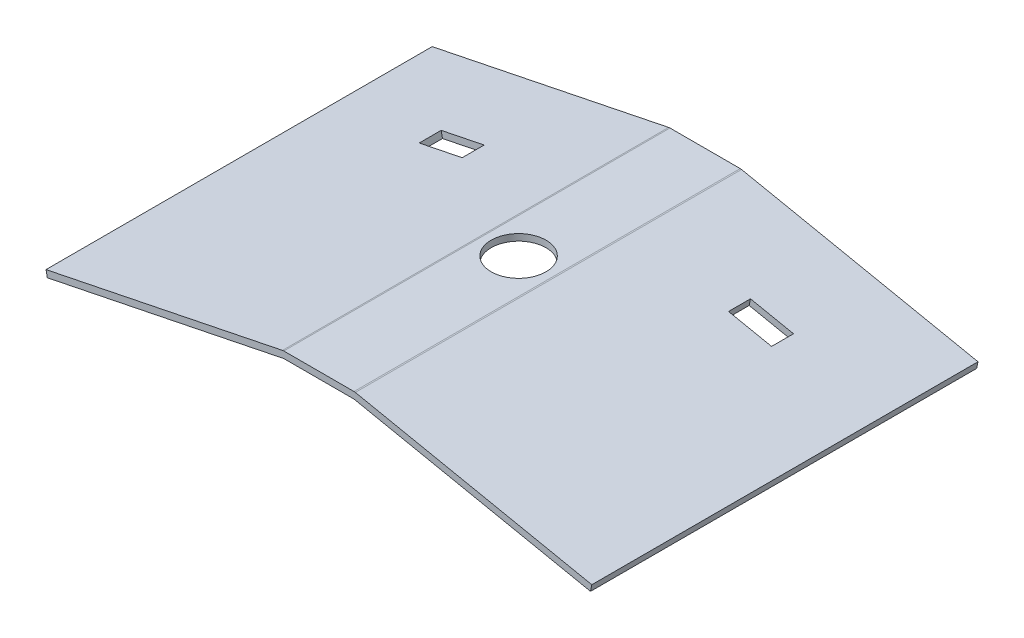
SolidWorks part; units mm, degrees
ref_plane "Front Plane" through (0, 0, 0) normal (0, 0, 1) x (1, 0, 0)
ref_plane "Top Plane" through (0, 0, 0) normal (0, 1, 0) x (1, 0, 0)
ref_plane "Right Plane" through (0, 0, 0) normal (1, 0, 0) x (0, 0, -1)
sketch "Sketch1" plane through (0, 0, 0) normal (0, 0, 1) x (1, 0, 0)
  line L0 (0, 0) -> (0, 19.9998) construction
  line L1 (-16, 19.9998) -> (16, 19.9998)
  line L2 (-113.9796, 0) -> (-113.9796, -10)
  line L4 (113.9796, 0) -> (113.9796, -10)
  line L6 (-113.9796, -7.3549) -> (0, 0) construction
  line L7 (0, 19.9998) -> (0, -10) construction
  line L8 (0, -10) -> (0, 0) construction
  line L9 (0, 0) -> (-113.9796, 0) construction
  line L10 (-113.9796, 0) -> (113.9796, 0) construction
  line L11 (-113.9796, 0) -> (-16, 19.9998)
  line L12 (16, 19.9998) -> (113.9796, 0)
  line L13 (-113.9796, -10) -> (113.9796, -10)
  point P0 (0, 0)
  dimension "D1" = 16
  dimension "D2" = 227.9593
  dimension "D3" = 100
  dimension "D4" = 10
extrude "Boss-Extrude1" add sketch "Sketch1" along normal blind 3
sketch "Sketch2" plane through (0, 0, 3) normal (0, 0, 1) x (1, 0, 0)
  line L0 (-16, 19.9998) -> (-123.7776, -2)
  line L1 (-16, 19.9998) -> (16, 19.9998)
  line L2 (-16, 22.9998) -> (16, 22.9998)
  line L3 (-16, 19.9998) -> (16, 19.9998)
  line L5 (-16, 22.9998) -> (16, 22.9998)
  line L7 (-16, 22.9998) -> (16, 22.9998)
  line L12 (-123.7776, -2) -> (-16, 19.9998)
  line L13 (-123.7776, -2) -> (-124.3776, 0.9394)
  line L15 (-124.3776, 0.9394) -> (-16.6, 22.9392)
  line L16 (-16.6, 22.9392) -> (-16, 22.9998)
  line L17 (16, 19.9998) -> (123.7776, -2)
  line L18 (123.7776, -2) -> (16, 19.9998)
  line L19 (123.7776, -2) -> (124.3776, 0.9394)
  line L21 (124.3776, 0.9394) -> (16.6, 22.9392)
  line L22 (16, 22.9998) -> (16.6, 22.9392)
  line M5 (113.9796, 0) -> (16, 19.9998)
  line M6 (16, 19.9998) -> (-16, 19.9998)
  line M7 (-16, 19.9998) -> (-113.9796, 0)
  dimension "D1" = 3
  dimension "D2" = 3
  dimension "D3" = 110
  dimension "D4" = 3
  dimension "D5" = 110
extrude "Boss-Extrude2" add sketch "Sketch2" along normal blind 88 and the other way blind 88 contours L22 L2 L16 L15 L13 L0 L17 L19 L21 M7 M6 M5
sketch "Sketch3" plane through (0, 0, 3) normal (0, 0, 1) x (1, 0, 0)
  line L6 (113.9796, 0) -> (16, 19.9998)
  line L7 (16, 19.9998) -> (-16, 19.9998)
  line L8 (-16, 19.9998) -> (-113.9796, 0)
  line L9 (-113.9796, 0) -> (-113.9796, -10)
  line L10 (-113.9796, -10) -> (113.9796, -10)
  line L11 (113.9796, -10) -> (113.9796, 0)
  line L12 (113.9796, 0) -> (16, 19.9998)
  line L13 (16, 19.9998) -> (-16, 19.9998)
  line L14 (-16, 19.9998) -> (-113.9796, 0)
  line L15 (-113.9796, 0) -> (-113.9796, -10)
  line L16 (-113.9796, -10) -> (113.9796, -10)
  line L17 (113.9796, -10) -> (113.9796, 0)
  dimension "D1" = 0
extrude "Cut-Extrude1" cut sketch "Sketch3" against normal blind 50
sketch "Sketch4" plane through (0, 22.9998, 0) normal (0, 1, 0) x (1, 0, 0)
  circle A0 centre (0, 0) radius 12.5
  dimension "D1" = 25
extrude "Cut-Extrude2" cut sketch "Sketch4" against normal through all
sketch "Sketch5" plane through (-5.1591, 25.2745, 0) normal (-0.2, 0.9798, 0) x (0.9798, 0.2, 0)
  line L0 (-121.6768, 85) -> (-121.6768, -91) construction
  line L1 (-76.6768, 45) -> (-56.6768, 45)
  line L2 (-76.6768, 45) -> (-76.6768, 35)
  line L3 (-76.6768, 35) -> (-56.6768, 35)
  line L4 (-56.6768, 45) -> (-56.6768, 35)
  line L5 (-121.6768, 85) -> (-11.6768, 85) construction
  dimension "D1" = 20
  dimension "D2" = 10
  dimension "D3" = 45
  dimension "D4" = 40
extrude "Cut-Extrude3" cut sketch "Sketch5" against normal through all
sketch "Sketch6" plane through (5.1591, 25.2745, 0) normal (0.2, 0.9798, 0) x (0.9798, -0.2, 0)
  line L0 (121.6768, 85) -> (121.6768, -91) construction
  line L1 (76.6768, 45) -> (56.6768, 45)
  line L2 (76.6768, 45) -> (76.6768, 35)
  line L3 (76.6768, 35) -> (56.6768, 35)
  line L4 (56.6768, 45) -> (56.6768, 35)
  line L5 (121.6768, 85) -> (11.6768, 85) construction
  dimension "D1" = 20
  dimension "D2" = 10
  dimension "D3" = 45
  dimension "D4" = 40
extrude "Cut-Extrude4" cut sketch "Sketch6" against normal through all
